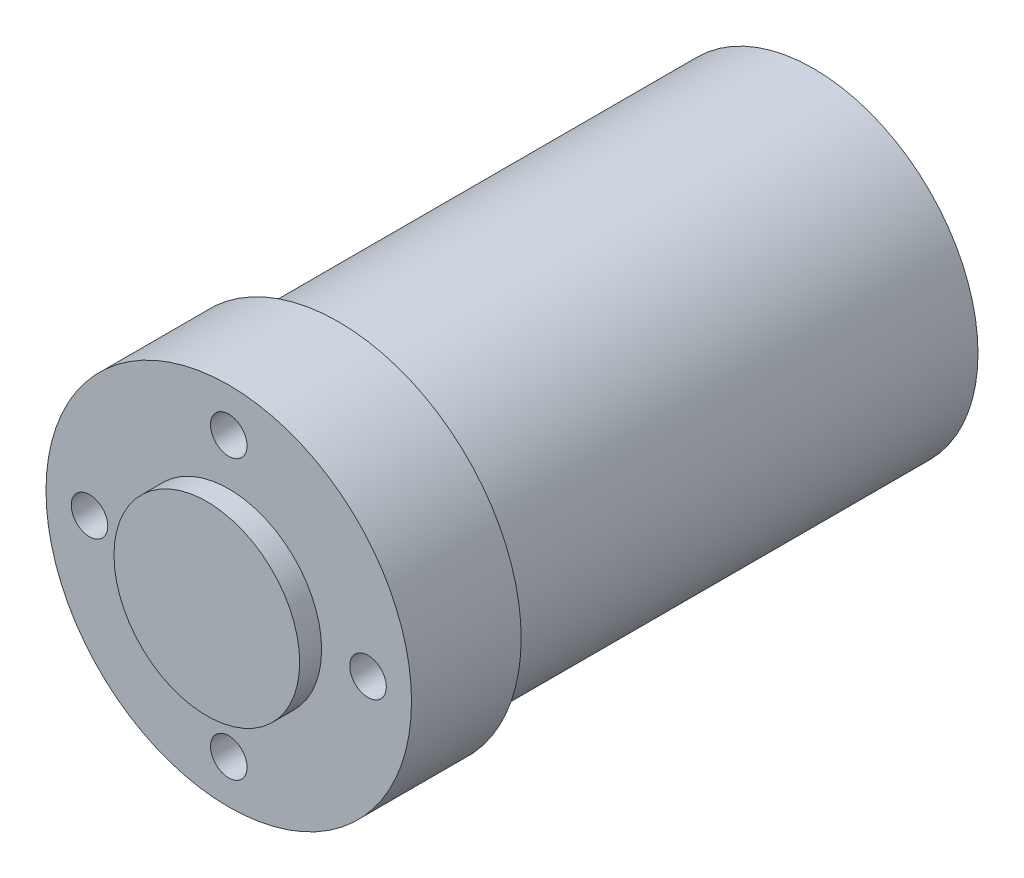
SolidWorks part; units mm, degrees
material "6061 Alloy"
ref_plane "Front Plane" through (0, 0, 0) normal (0, 0, 1) x (1, 0, 0)
ref_plane "Top Plane" through (0, 0, 0) normal (0, 1, 0) x (1, 0, 0)
ref_plane "Right Plane" through (0, 0, 0) normal (1, 0, 0) x (0, 0, -1)
ref_plane "Plane1" through (0, 0, 0) normal (0, -1, 0) x (1, 0, 0)
sketch "Sketch1" plane through (0, 0, 0) normal (0, -1, 0) x (1, 0, 0)
  line L0 (25, 80) -> (0, 80)
  line L1 (0, 80) -> (0, 65)
  line L2 (0, 65) -> (25, 65)
  line L3 (25, 65) -> (25, 80)
  line L4 (0, 80) -> (0, 65) construction
revolve "Revolve1" add sketch "Sketch1" angle 360 about L4
sketch "Sketch2" plane through (0, 0, 80) normal (0, 0, 1) x (1, 0, 0)
  circle A0 centre (0, 0) radius 12.7
extrude "Boss-Extrude1" add sketch "Sketch2" along normal blind 3
sketch "Sketch3" plane through (0, 0, 65) normal (0, 0, -1) x (-1, 0, 0)
  circle A0 centre (0, 0) radius 22.4917
extrude "Boss-Extrude2" add sketch "Sketch3" along normal blind 65
hole_wizard "#10 Clearance Hole1" positions "Sketch5" profile "Sketch4" hole size "#10" standard "ANSI Inch"
sketch "Sketch5" plane through (0, 0, 0) normal (0, 0, -1) x (-1, 0, 0)
  point P0 (-12.3744, 12.3744)
  point P1 (-17.5, 0)
  point P2 (-12.3744, -12.3744)
  point P3 (0, -17.5)
  point P4 (12.3744, -12.3744)
  point P5 (17.5, 0)
  point P6 (12.3744, 12.3744)
  point P7 (0, 17.5)
sketch "Sketch4" plane through (12.3744, 12.3744, 0) normal (1, 0, 0) x (0, 1, 0)
  line L0 (0, 0) -> (0, 8)
  line L1 (0, 8) -> (2.5, 8)
  line L2 (2.5, 8) -> (2.5, 0)
  line L5 (2.5, 0) -> (0, 0)
  line L10 (0, 8) -> (-2.5, 8) construction
  line L11 (0, -6.35) -> (0, 107.95) construction
  dimension "Hole Dia." = 5
  dimension "Hole Depth" = 8
  dimension "Drill Angle" = 180
hole_wizard "#10 Clearance Hole2" positions "Sketch7" profile "Sketch6" hole size "#10" standard "ANSI Inch"
sketch "Sketch7" plane through (0, 0, 80) normal (0, 0, 1) x (1, 0, 0)
  point P0 (-19.05, 0)
  point P1 (0, -19.05)
  point P2 (19.05, 0)
  point P3 (0, 19.05)
sketch "Sketch6" plane through (-19.05, 0, 80) normal (1, 0, 0) x (0, -1, 0)
  line L0 (0, 0) -> (0, 12.446)
  line L1 (0, 12.446) -> (2.5, 12.446)
  line L2 (2.5, 12.446) -> (2.5, 0)
  line L5 (2.5, 0) -> (0, 0)
  line L10 (0, 12.446) -> (-2.5, 12.446) construction
  line L11 (0, -6.35) -> (0, 107.95) construction
  dimension "Hole Dia." = 5
  dimension "Hole Depth" = 12.446
  dimension "Drill Angle" = 180
sketch "Sketch8" plane through (0, 0, 0) normal (0, 0, -1) x (-1, 0, 0)
  circle A0 centre (0, 0) radius 6.35
  dimension "D1" = 12.7
